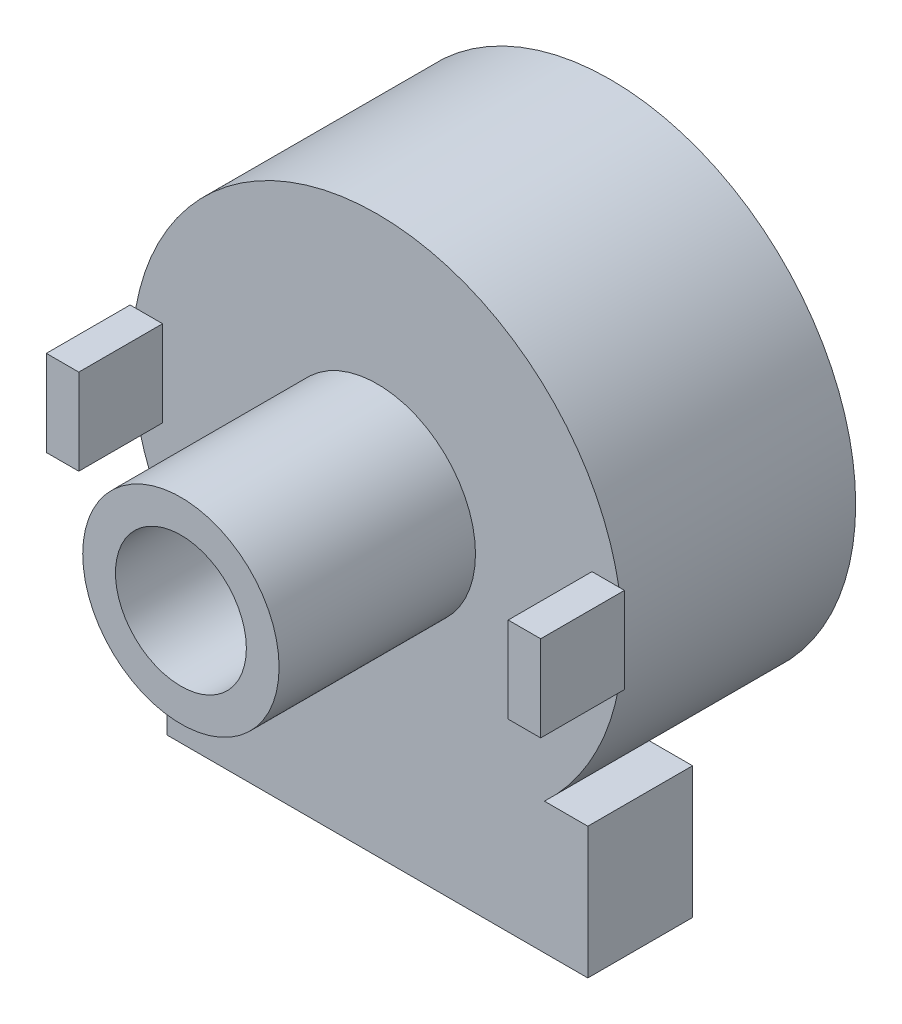
SolidWorks part; units mm, degrees
ref_plane "Front Plane" through (0, 0, 0) normal (0, 0, 1) x (1, 0, 0)
ref_plane "Top Plane" through (0, 0, 0) normal (0, 1, 0) x (1, 0, 0)
ref_plane "Right Plane" through (0, 0, 0) normal (1, 0, 0) x (0, 0, -1)
sketch "Sketch1" plane through (0, 0, 0) normal (0, 0, 1) x (1, 0, 0)
  circle A0 centre (0, 0) radius 11.8999
  dimension "D1" = 23.7998
extrude "Body" add sketch "Sketch1" against normal blind 11.303
sketch "Sketch2" plane through (0, 0, 0) normal (0, 0, 1) x (1, 0, 0)
  circle A0 centre (0, 0) radius 4.7625
  dimension "D1" = 9.525
extrude "bushing" add sketch "Sketch2" along normal blind 9.525
sketch "Sketch3" plane through (0, 0, 0) normal (0, 0, 1) x (1, 0, 0)
  line L0 (0, -6.2167) -> (0, 6.2167) construction
  line L1 (-11.9888, -2.0828) -> (-10.414, -2.0828)
  line L2 (-11.9888, -2.0828) -> (-11.9888, 2.0828)
  line L3 (-11.9888, 2.0828) -> (-10.414, 2.0828)
  line L4 (-10.414, -2.0828) -> (-10.414, 2.0828)
  line L5 (-11.9888, -2.0828) -> (-10.414, 2.0828) construction
  line L6 (-11.9888, 2.0828) -> (-10.414, -2.0828) construction
  line L7 (10.414, 2.0828) -> (11.9888, 2.0828)
  line L8 (10.414, 2.0828) -> (10.414, -2.0828)
  line L9 (10.414, -2.0828) -> (11.9888, -2.0828)
  line L10 (11.9888, 2.0828) -> (11.9888, -2.0828)
  line L11 (10.414, 2.0828) -> (11.9888, -2.0828) construction
  line L12 (10.414, -2.0828) -> (11.9888, 2.0828) construction
  line L13 (6.2167, 0) -> (-6.2167, 0) construction
  point P0 (-11.2014, 0)
  point P5 (11.2014, 0)
  dimension "D1" = 10.414
  dimension "D2" = 1.5748
  dimension "D3" = 4.1656
  dimension "D4" = 10.414
  dimension "D5" = 1.5748
  dimension "D6" = 4.1656
extrude "mount tab" add sketch "Sketch3" along normal blind 4.064
sketch "Sketch4" plane through (0, 0, 9.525) normal (0, 0, 1) x (1, 0, 0)
  circle A0 centre (0, 0) radius 3.175
  dimension "D1" = 6.35
extrude "Cut-Extrude1" cut sketch "Sketch4" against normal blind 9.525
sketch "Sketch5" plane through (0, 0, 0) normal (0, 0, 1) x (1, 0, 0)
  line L0 (6.2167, 0) -> (-6.2167, 0) construction
  line L1 (-10.2108, -8.7122) -> (10.2108, -8.7122)
  line L2 (-10.2108, -8.7122) -> (-10.2108, -15.0876)
  line L3 (-10.2108, -15.0876) -> (10.2108, -15.0876)
  line L4 (10.2108, -8.7122) -> (10.2108, -15.0876)
  line L5 (-10.2108, -8.7122) -> (10.2108, -15.0876) construction
  line L6 (-10.2108, -15.0876) -> (10.2108, -8.7122) construction
  line L7 (0, -6.2167) -> (0, 6.2167) construction
  circle A0 centre (0, 0) radius 11.8999 construction
  point P0 (0, -11.8999)
  dimension "D1" = 15.0876
  dimension "D2" = 20.4216
extrude "board" add sketch "Sketch5" against normal blind 5.08
